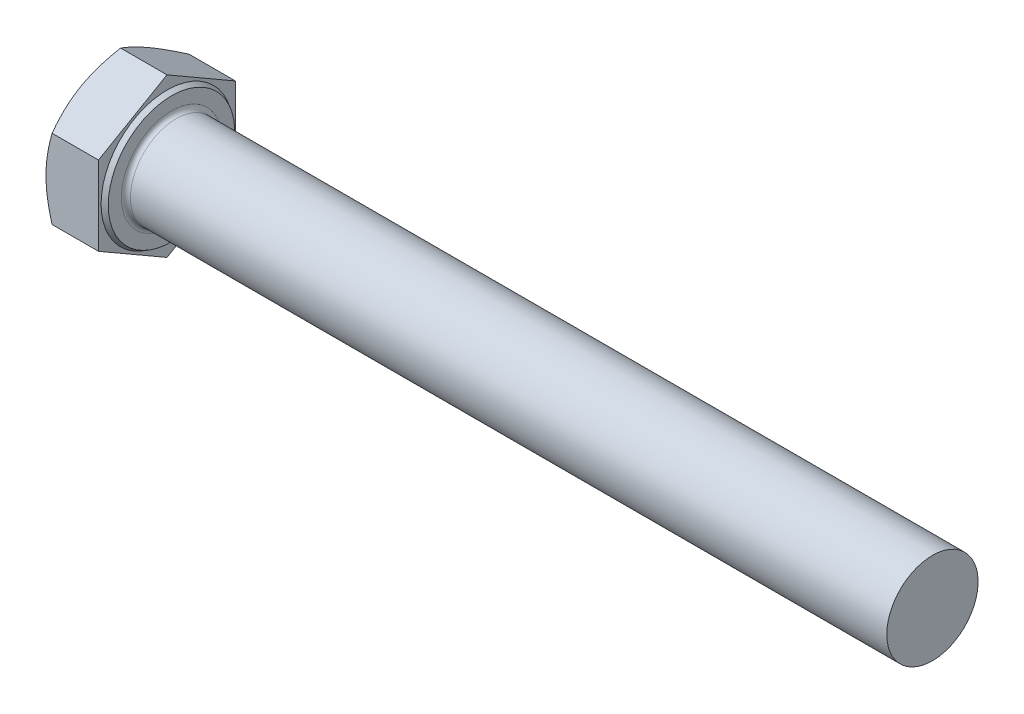
SolidWorks part; units mm, degrees
ref_plane "前视" through (0, 0, 0) normal (0, 0, 1) x (1, 0, 0)
ref_plane "上视" through (0, 0, 0) normal (0, 1, 0) x (1, 0, 0)
ref_plane "右视" through (0, 0, 0) normal (1, 0, 0) x (0, 0, -1)
sketch "草图1" plane through (0, 0, 0) normal (1, 0, 0) x (0, 0, -1)
  line L0 (9, 5.1962) -> (9, -5.1962)
  line L1 (-9, 5.1962) -> (-9, -5.1962)
  line L2 (9, -5.1962) -> (0, -10.3923)
  line L3 (0, -10.3923) -> (-9, -5.1962)
  line L4 (9, 5.1962) -> (0, 10.3923)
  line L5 (0, 10.3923) -> (-9, 5.1962)
  circle A0 centre (0, 0) radius 10.015 construction
  dimension "e" = 20.03
  dimension "s" = 18
  dimension "D2" = 120
  dimension "D3" = 9
  dimension "D4" = 9
  dimension "D5" = 9
extrude "基体-拉伸" add sketch "草图1" along normal blind 7.5
sketch "草图2" plane through (0, 0, 0) normal (0, 0, 1) x (1, 0, 0)
  line L0 (0, 5.1962) -> (0, -5.1962) construction
  line L1 (0, 0) -> (107.5, 0)
  line L2 (0, 0) -> (0, 6)
  line L3 (0, 6) -> (77.5, 6)
  line L4 (107.5, 0) -> (107.5, 4.4845)
  line L5 (7.5, 10.3923) -> (7.5, 5.1962) construction
  line L7 (0, 0) -> (119.5, 0) construction
  line L8 (107.5, -4.4845) -> (77.5, -6) construction
  line L9 (0, -6) -> (77.5, -6) construction
  line L10 (9.25, 6) -> (9.25, 0) construction
  line L11 (77.5, 15.24) -> (77.5, -1.27) construction
  line L12 (7.5, 5.1962) -> (7.5, -5.1962) construction
  line L13 (77.5, 6) -> (107.5, 6)
  line L14 (107.5, 6) -> (107.5, 4.4845)
  dimension "l" = 100
  dimension "d" = 12
  dimension "Minor_dia" = 8.969
  dimension "p" = 1.75
  dimension "b" = 30
  dimension "ds" = 12
revolve "凸台-旋转1" add sketch "草图2" angle 360 about L7
cosmetic thread "螺旋线1" parameters "Thread_length"=30, "Thread_minor"=8.969
sketch "草图3" plane through (0, 0, 0) normal (0, 0, 1) x (1, 0, 0)
  line L0 (0, 9) -> (3.6906, 15.3923)
  line L1 (0, 10.3923) -> (0, 5.1962) construction
  line L2 (3.6906, 15.3923) -> (3.6906, 20.3923)
  line L3 (3.6906, 20.3923) -> (-10, 20.3923)
  line L4 (-10, 20.3923) -> (-10, 9)
  line L5 (-10, 9) -> (0, 9)
  line L6 (0, 0) -> (99.06, 0) construction
  line L7 (7.5, 10.3923) -> (0, 10.3923) construction
  dimension "D1" = 9
  dimension "D2" = 5
  dimension "D3" = 10
  dimension "D4" = 5
  dimension "Head_ch_ang" = 30
revolve "切除-旋转1" cut sketch "草图3" angle 360 about L6
sketch "草图4" plane through (0, 0, 0) normal (0, 0, 1) x (1, 0, 0)
  line L0 (7.5, 0) -> (7.5, 8.315) construction
  line L2 (7.5, -6) -> (7.5, 6) construction
  line L3 (7.5, 10.3923) -> (7.5, 5.1962) construction
  line L4 (7.5, 8.315) -> (6.9, 8.6614)
  line L5 (0, 0) -> (95.25, 0) construction
  line L6 (0, 0) -> (119.5, 0) construction
  line L9 (6.9, 8.6614) -> (6.9, 10.3923)
  line L10 (7.5, 10.3923) -> (0.8038, 10.3923) construction
  line L11 (6.9, 10.3923) -> (7.5, 10.3923)
  line L12 (7.5, 10.3923) -> (7.5, 8.315)
  dimension "D1" = 120
  dimension "c" = 0.6
  dimension "dw" = 16.63
revolve "切除-旋转3" cut sketch "草图4" angle 360 about L5
fillet "圆角" radius 0.6 1 edges at (7.5, 0, -6)
sketch "草图6" plane through (0, 0, 0) normal (0, 0, 1) x (1, 0, 0)
  line L0 (0, 0) -> (107.5, 0) construction
  line L1 (107.5, -6) -> (107.5, 6) construction
  line L2 (107.5, 0) -> (107.5, 6) construction
  line L4 (106.625, 6) -> (108.375, 6)
  line L5 (106.625, 6) -> (107.5, 4.4845)
  line L6 (107.5, 4.4845) -> (108.375, 6)
  dimension "D1" = 1.75
revolve "切除-旋转4" [suppressed] cut sketch "草图6" angle 360 about L0
pattern_linear "阵列(线性)1" [suppressed]
